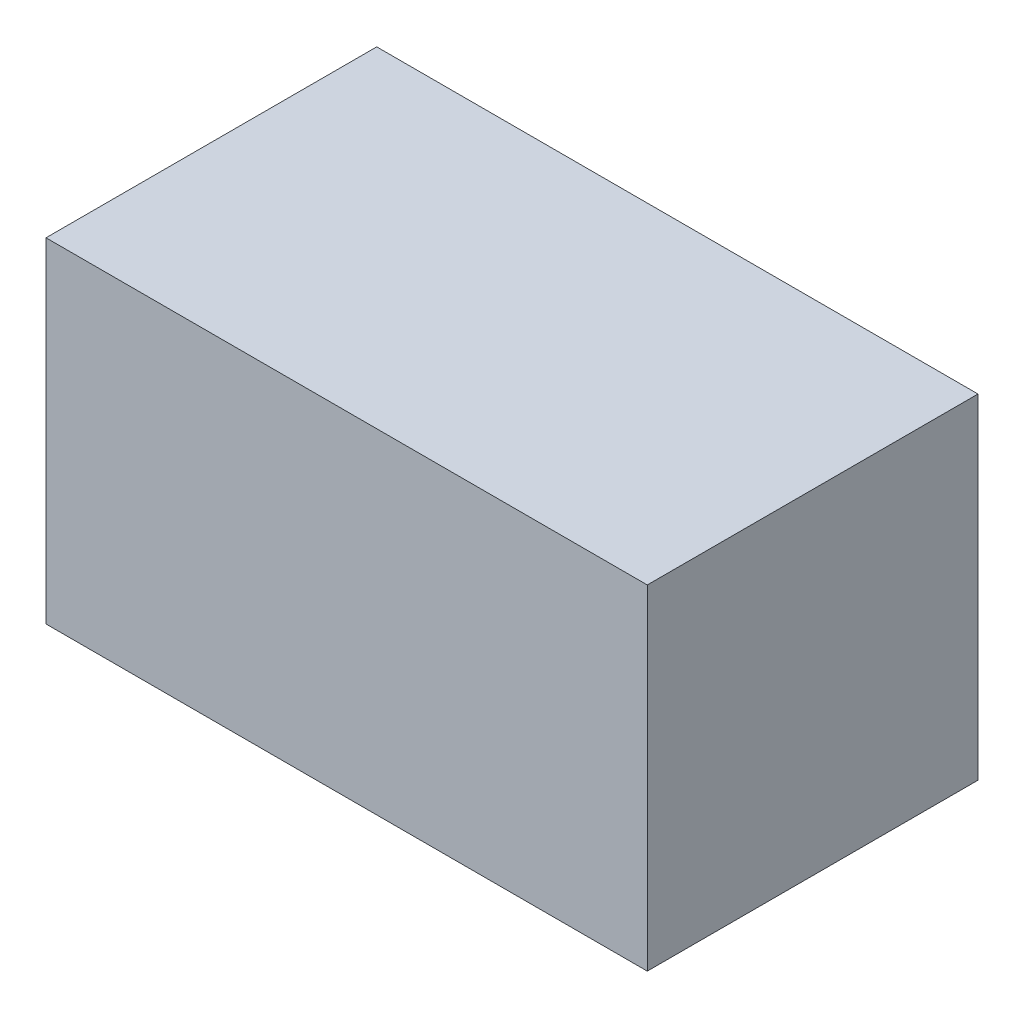
SolidWorks part; units mm, degrees
ref_plane "Front Plane" through (0, 0, 0) normal (0, 0, 1) x (1, 0, 0)
ref_plane "Top Plane" through (0, 0, 0) normal (0, 1, 0) x (1, 0, 0)
ref_plane "Right Plane" through (0, 0, 0) normal (1, 0, 0) x (0, 0, -1)
sketch "Sketch2" plane through (0, 0, 0) normal (0, 1, 0) x (1, 0, 0)
  line L1 (-8, -4.4) -> (8, -4.4)
  line L2 (-8, -4.4) -> (-8, 4.4)
  line L3 (-8, 4.4) -> (8, 4.4)
  line L4 (8, -4.4) -> (8, 4.4)
  line L5 (-8, -4.4) -> (8, 4.4) construction
  line L6 (-8, 4.4) -> (8, -4.4) construction
  point P0 (0, 0)
  dimension "D1" = 16
  dimension "D2" = 8.8
extrude "Boss-Extrude1" add sketch "Sketch2" along normal blind 8.9
